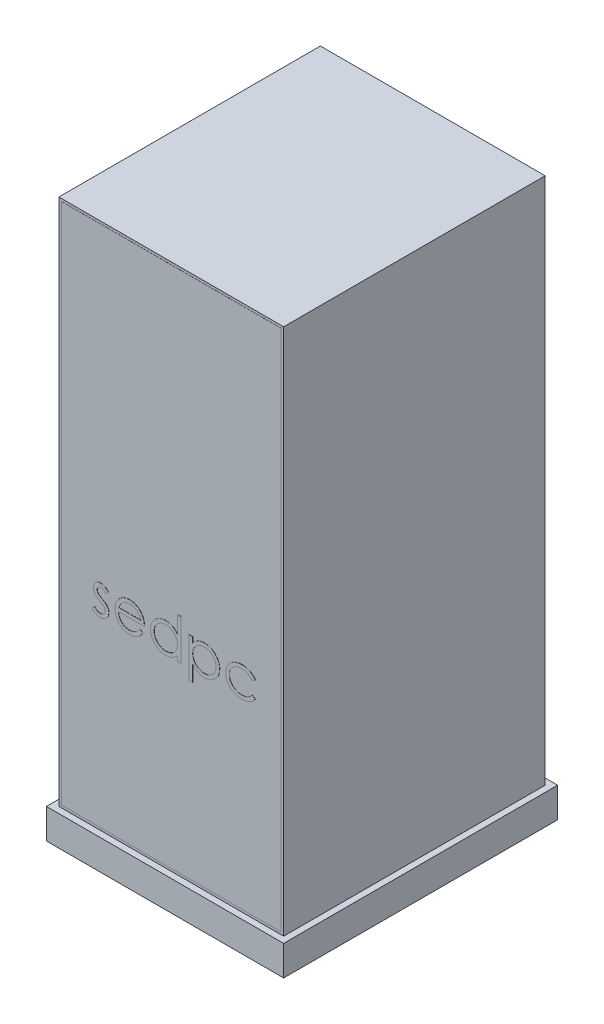
SolidWorks part; units mm, degrees
ref_plane "Alzado" through (0, 0, 0) normal (0, 0, 1) x (1, 0, 0)
ref_plane "Planta" through (0, 0, 0) normal (0, 1, 0) x (1, 0, 0)
ref_plane "Vista lateral" through (0, 0, 0) normal (1, 0, 0) x (0, 0, -1)
sketch "Croquis1" plane through (0, 0, 0) normal (0, 0, 1) x (1, 0, 0)
  line L1 (-450, 1056.5) -> (450, 1056.5)
  line L2 (-450, 1056.5) -> (-450, -1056.5)
  line L3 (-450, -1056.5) -> (450, -1056.5)
  line L4 (450, 1056.5) -> (450, -1056.5)
  line L5 (-450, 1056.5) -> (450, -1056.5) construction
  line L6 (-450, -1056.5) -> (450, 1056.5) construction
  point P0 (0, 0)
  dimension "D1" = 2113
  dimension "D2" = 900
extrude "Saliente-Extruir1" add sketch "Croquis1" along normal blind 1047
shell "Vaciado1" thickness 10
sketch "Croquis9" plane through (0, 0, 1047) normal (0, 0, 1) x (1, 0, 0)
  line L0 (-440, 1046.5) -> (440, 1046.5)
  line L1 (440, 1046.5) -> (440, -1046.5)
  line L2 (440, -1046.5) -> (-440, -1046.5)
  line L3 (-440, -1046.5) -> (-440, 1046.5)
extrude "Saliente-Extruir5" add sketch "Croquis9" along normal blind 0.3 separate body
sketch "Croquis10" plane through (0, 0, 1047) normal (0, 0, -1) x (-1, 0, 0)
  line L0 (107.9806, 0) -> (-99.6636, 0)
  line L1 (-99.6636, 0) -> (20.1235, 235.7502)
  line L2 (20.1235, 235.7502) -> (107.9806, 0)
  line L3 (47.6966, 86.2289) -> (21.4865, 63.6321)
  line L4 (21.4865, 63.6321) -> (46.547, 34.5643)
  line L5 (46.547, 34.5643) -> (4.5872, 63.6321)
  line L6 (4.5872, 63.6321) -> (27.7047, 97.0026)
  line L7 (27.7047, 97.0026) -> (4.5872, 113.0175)
  line L8 (4.5872, 113.0175) -> (20.1235, 163.6851)
  line L9 (20.1235, 163.6851) -> (47.6966, 86.2289)
extrude "Cortar-Extruir5" cut sketch "Croquis10" against normal blind 0.2
sketch "Croquis14" plane through (0, 0, 1047) normal (0, 0, 1) x (1, 0, 0)
  line L0 (-329.8691, -353.8859) -> (310.6907, -353.8859) construction
  text T0 "sedpc" font "Century Gothic" height in points 600
extrude "Saliente-Extruir6" add sketch "Croquis14" along normal blind 1
sketch "Croquis15" plane through (0, -1056.5, 0) normal (0, -1, 0) x (1, 0, 0)
  line L0 (0, 0) -> (0, 1047) construction
  line L1 (-450, 1047) -> (450, 1047) construction
  line L2 (0, 1047) -> (0, 523.5) construction
  line L3 (0, 523.5) -> (-450, 523.5) construction
  line L4 (-450, 1047) -> (-450, 0) construction
  line L5 (450, 1047) -> (450, 0) construction
  line L6 (475, -25) -> (-475, -25)
  line L7 (475, -25) -> (475, 1072)
  line L8 (475, 1072) -> (-475, 1072)
  line L9 (-475, -25) -> (-475, 1072)
  line L10 (475, -25) -> (-475, 1072) construction
  line L11 (475, 1072) -> (-475, -25) construction
  line L12 (-450, 0) -> (450, 0) construction
  dimension "D1" = 25
  dimension "D2" = 25
extrude "Saliente-Extruir7" add sketch "Croquis15" along normal blind 120
